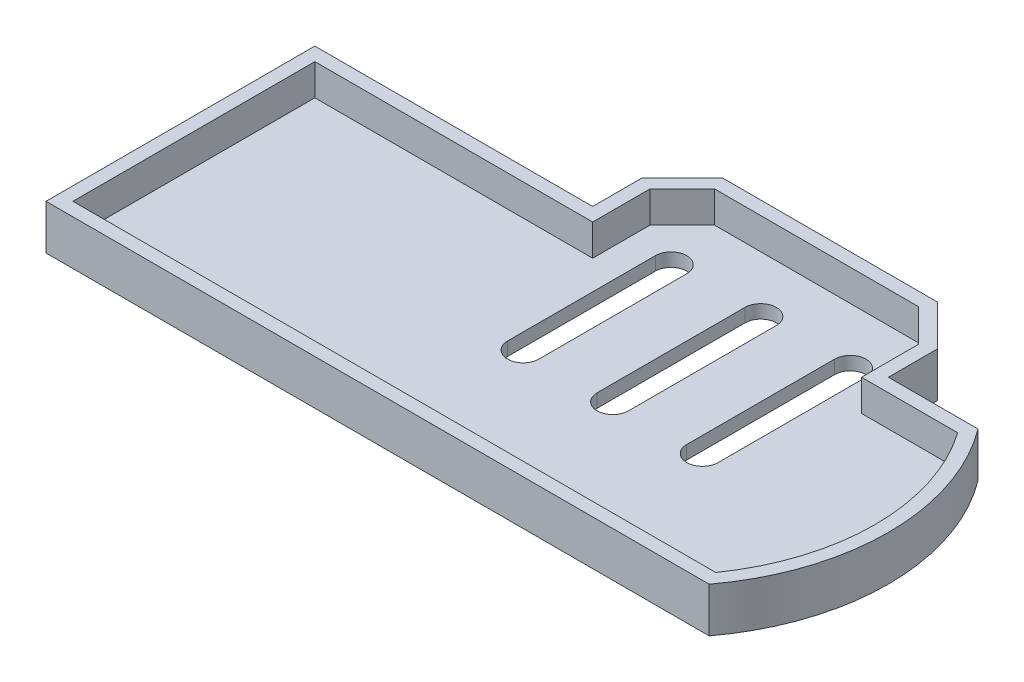
SolidWorks part; units mm, degrees
material "3.1355 (EN-AW 2024)"
ref_plane "Front" through (0, 0, 0) normal (0, 0, 1) x (1, 0, 0)
ref_plane "Top" through (0, 0, 0) normal (0, 1, 0) x (1, 0, 0)
ref_plane "Right" through (0, 0, 0) normal (1, 0, 0) x (0, 0, -1)
sketch "Эскиз1" plane through (0, 0, 0) normal (0, 1, 0) x (1, 0, 0)
  line L0 (0, 0) -> (190, 0) construction
  line L1 (0, 0) -> (0, 60)
  line L2 (95, 0) -> (95, 28) construction
  line L3 (119, 80) -> (71, 80)
  line L4 (95, 80) -> (95, 68) construction
  line L5 (95, 64.5) -> (95, 31.5) construction
  line L6 (98.5, 64.5) -> (98.5, 31.5)
  line L7 (91.5, 64.5) -> (91.5, 31.5)
  line L8 (75, 64.5) -> (75, 31.5) construction
  line L9 (78.5, 64.5) -> (78.5, 31.5)
  line L10 (71.5, 64.5) -> (71.5, 31.5)
  line L11 (95, 64.5) -> (75, 64.5) construction
  line L12 (95, 31.5) -> (75, 31.5) construction
  line L13 (115, 64.5) -> (115, 31.5) construction
  line L14 (111.5, 64.5) -> (111.5, 31.5)
  line L15 (118.5, 64.5) -> (118.5, 31.5)
  line L16 (0, 60) -> (62, 60)
  line L17 (62, 60) -> (62, 71)
  line L18 (62, 71) -> (71, 80)
  line L19 (128, 60) -> (148, 60)
  line L21 (128, 60) -> (128, 71)
  line L22 (128, 71) -> (119, 80)
  line L23 (0, 0) -> (148, 0)
  line L24 (148, 60) -> (148, 0) construction
  arc A0 (98.5, 64.5) -> (91.5, 64.5) centre (95, 64.5) ccw
  arc A1 (91.5, 31.5) -> (98.5, 31.5) centre (95, 31.5) ccw
  arc A2 (78.5, 64.5) -> (71.5, 64.5) centre (75, 64.5) ccw
  arc A3 (71.5, 31.5) -> (78.5, 31.5) centre (75, 31.5) ccw
  arc A4 (111.5, 64.5) -> (118.5, 64.5) centre (115, 64.5) cw
  arc A5 (118.5, 31.5) -> (111.5, 31.5) centre (115, 31.5) cw
  arc A6 (148, 0) -> (148, 60) centre (108, 30) ccw
  point P11 (95, 48)
  point P18 (75, 48)
  point P29 (115, 48)
  point P40 (0, 0)
  point P41 (0, 0)
  dimension "D14" = 50
  dimension "D1" = 60
  dimension "D2" = 190
  dimension "D3" = 28
  dimension "D4" = 80
  dimension "D5" = 12
  dimension "D6" = 7
  dimension "D7" = 7
  dimension "D8" = 62
  dimension "D9" = 20
  dimension "D10" = 45
  dimension "D11" = 11
  dimension "D12" = 148
  dimension "D13" = 66
extrude "Бобышка-Вытянуть1" add sketch "Эскиз1" along normal blind 10
sketch "Эскиз3" plane through (0, 10, 0) normal (0, 1, 0) x (1, 0, 0)
  line L3 (125, 57) -> (125, 69.7574)
  line L4 (125, 69.7574) -> (117.7574, 77)
  line L5 (117.7574, 77) -> (72.2426, 77)
  line L6 (72.2426, 77) -> (65, 69.7574)
  line L7 (65, 69.7574) -> (65, 57)
  line L8 (65, 57) -> (3, 57)
  line L9 (3, 57) -> (3, 3)
  line L11 (0, 3) -> (146.4708, 3)
  line L12 (146.4708, 57) -> (128, 57)
  line L13 (3, 3) -> (146.4708, 3)
  line L14 (146.4708, 57) -> (125, 57)
  arc A2 (146.4708, 3) -> (146.4708, 57) centre (108, 30) ccw
  arc A3 (146.4708, 3) -> (146.4708, 57) centre (108, 30) ccw
  dimension "D1" = 3
extrude "Вырез-Вытянуть1" cut sketch "Эскиз3" against normal blind 7
